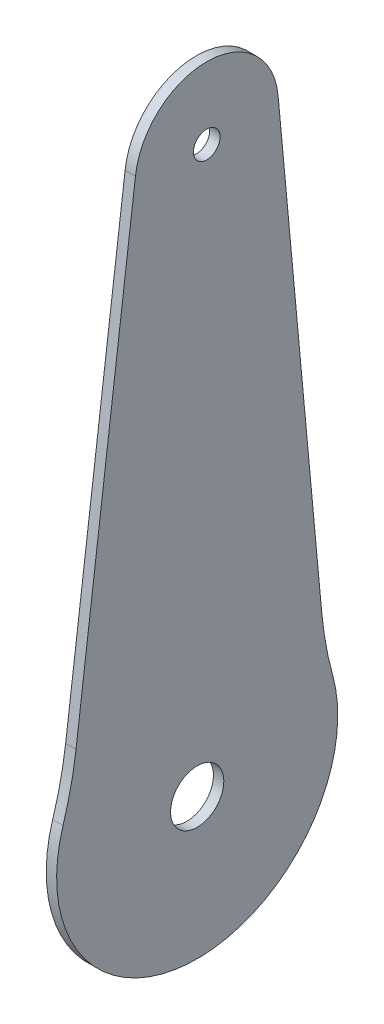
SolidWorks part; units mm, degrees
ref_plane "前基準面" through (0, 0, 0) normal (0, 0, 1) x (1, 0, 0)
ref_plane "上基準面" through (0, 0, 0) normal (0, 1, 0) x (1, 0, 0)
ref_plane "右基準面" through (0, 0, 0) normal (1, 0, 0) x (0, 0, -1)
sketch "草圖2" plane through (0, 0, 0) normal (1, 0, 0) x (0, 0, -1)
  line L0 (11.7185, 46.2767) -> (18.0121, -21.4416)
  line L1 (-8.93, 46.628) -> (-17.523, -20.8372)
  circle A0 centre (0, -35.5155) radius 3.85
  circle A7 centre (1.3776, 45.4728) radius 1.925
  arc A8 (-20.0208, -31.9867) -> (20.1292, -32.6696) centre (0, -35.5155) ccw
  arc A9 (-19.4024, -29.4465) -> (19.5975, -30.1099) centre (0, -35.5155) ccw
  arc A10 (11.7185, 46.2767) -> (-8.93, 46.628) centre (1.3776, 45.4728) ccw
  arc A11 (18.0121, -21.4416) -> (19.5975, -30.1099) centre (67.7975, -16.8147) ccw
  arc A12 (-19.4024, -29.4465) -> (-17.523, -20.8372) centre (-67.1223, -14.5197) ccw
extrude "填料-伸長1" add sketch "草圖2" along normal blind 1.5
